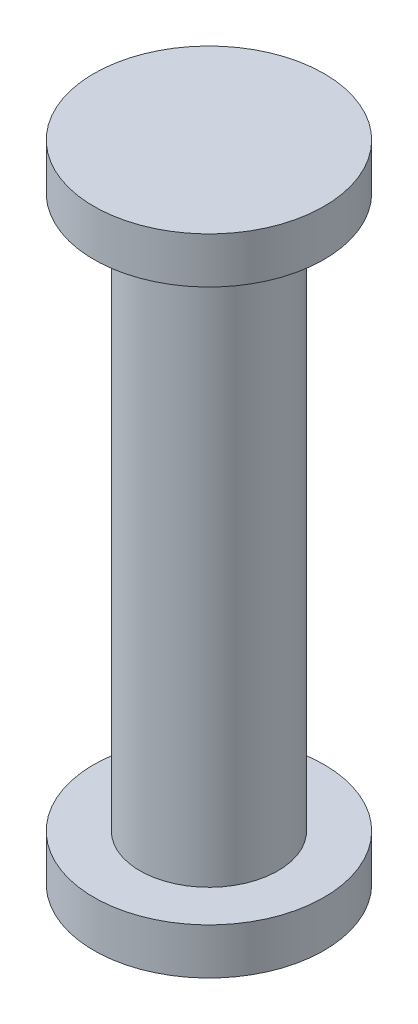
SolidWorks part; units mm, degrees
ref_plane "Front Plane" through (0, 0, 0) normal (0, 0, 1) x (1, 0, 0)
ref_plane "Top Plane" through (0, 0, 0) normal (0, 1, 0) x (1, 0, 0)
ref_plane "Right Plane" through (0, 0, 0) normal (1, 0, 0) x (0, 0, -1)
sketch "Sketch1" plane through (0, 0, 0) normal (0, 0, 1) x (1, 0, 0)
  line L0 (0, 0) -> (0, 14)
  line L1 (0, 14) -> (-2.5, 14)
  line L2 (-2.5, 14) -> (-2.5, 13)
  line L3 (-2.5, 13) -> (-1.5, 13)
  line L4 (-1.5, 13) -> (-1.5, 1)
  line L5 (-1.5, 1) -> (-2.5, 1)
  line L6 (-2.5, 1) -> (-2.5, 0)
  line L7 (-2.5, 0) -> (0, 0)
  dimension "D1" = 14
  dimension "D2" = 1
  dimension "D3" = 1
  dimension "D4" = 2.5
  dimension "D5" = 1.5
revolve "Revolve1" add sketch "Sketch1" angle 360 about L0
